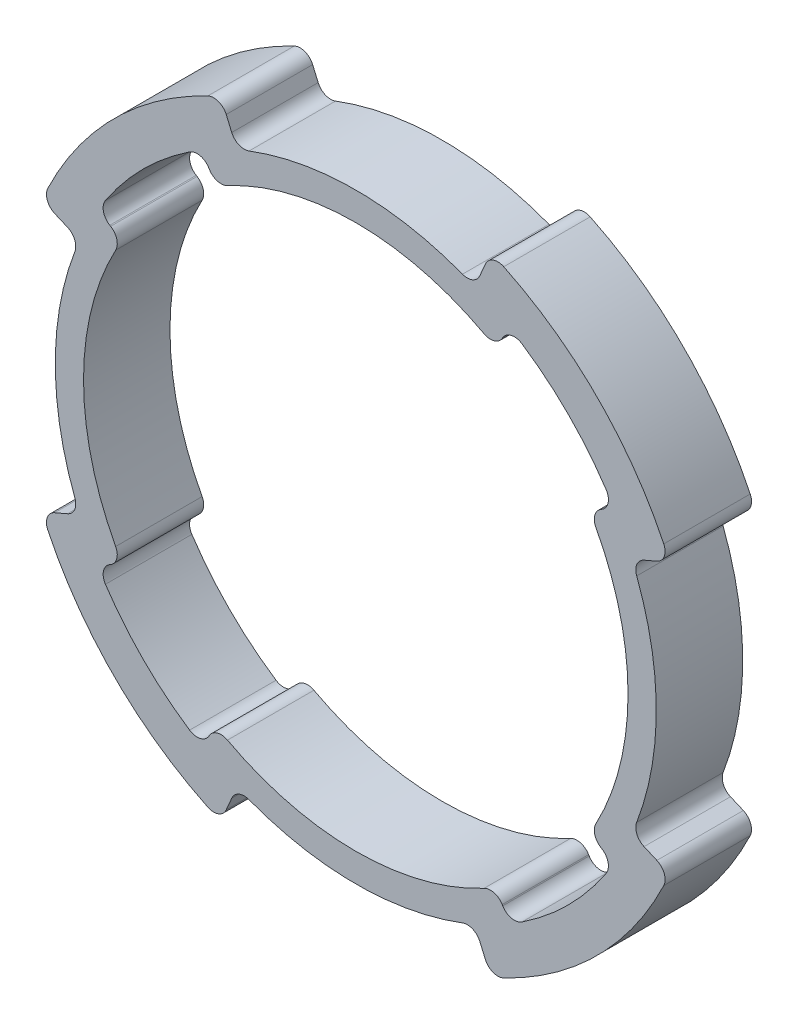
SolidWorks part; units mm, degrees
ref_plane "Front Plane" through (0, 0, 0) normal (0, 0, 1) x (1, 0, 0)
ref_plane "Top Plane" through (0, 0, 0) normal (0, 1, 0) x (1, 0, 0)
ref_plane "Right Plane" through (0, 0, 0) normal (1, 0, 0) x (0, 0, -1)
sketch "Sketch1" plane through (0, 0, 0) normal (0, 0, 1) x (1, 0, 0)
  circle A0 centre (0, 0) radius 50.2
  circle A1 centre (0, 0) radius 40
  dimension "D1" = 100.4
  dimension "D2" = 80
extrude "Boss-Extrude1" add sketch "Sketch1" along normal blind 12.7
sketch "Sketch2" plane through (0, 0, 0) normal (0, 0, -1) x (-1, 0, 0)
  line L0 (-37.9034, 22.6397) -> (0, 0)
  line L1 (-22.6397, 37.9034) -> (0, 0)
  line L2 (0, 46.99) -> (0, 0) construction
  line L3 (-46.99, 0) -> (0, 0) construction
  line L4 (0, 0) -> (-31.2188, 31.2188) construction
  line L5 (-37.9034, 22.6397) -> (-43.0974, 25.7421) construction
  line L6 (-41.7185, 21.424) -> (-40.1801, 23.9996) construction
  line L7 (-41.7185, 21.424) -> (-40.5064, 20.7001) construction
  line L8 (-40.5547, 17.451) -> (-46.1121, 19.8423) construction
  line L9 (-40.5547, 17.451) -> (0, 0) construction
  line L10 (-42.3338, 20.3938) -> (-43.9149, 16.7196) construction
  line L11 (-46.1121, 19.8423) -> (-40.5547, 17.451)
  line L12 (-46.1121, -19.8423) -> (-40.5547, -17.451)
  circle A0 centre (0, 0) radius 44.15 construction
  circle A2 centre (0, 0) radius 50.2 construction
  circle A4 centre (-42.3338, 20.3938) radius 1.2 construction
  arc A5 (-46.1121, 19.8423) -> (-46.1121, -19.8423) centre (0, 0) ccw
  arc A6 (-40.5547, 17.451) -> (-40.5547, -17.451) centre (0, 0) ccw
  arc A7 (-22.6397, 37.9034) -> (-37.9034, 22.6397) centre (0, 0) ccw
  point P20 (-43.1243, 18.5567)
  dimension "D1" = 45
  dimension "D2" = 3
extrude "Cut-Extrude1" cut sketch "Sketch2" against normal through all
fillet "Fillet1" radius 2 8 edges at (22.6397, 37.9034, 6.35) (20.5116, 34.3406, 6.35) (37.9034, 22.6397, 6.35) (34.3406, 20.5116, 6.35) (46.1121, -19.8423, 6.35) (40.5547, -17.451, 6.35) (46.1121, 19.8423, 6.35) (40.5547, 17.451, 6.35)
pattern_circular "CirPattern1" count 4 over 360 about axis through (0, 0, 0) along (0, 0, 1) of "Cut-Extrude1", "Fillet1"
